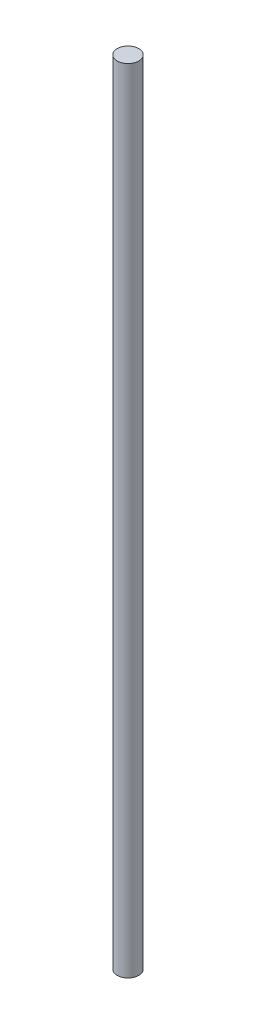
SolidWorks part; units mm, degrees
ref_plane "Front Plane" through (0, 0, 0) normal (0, 0, 1) x (1, 0, 0)
ref_plane "Top Plane" through (0, 0, 0) normal (0, 1, 0) x (1, 0, 0)
ref_plane "Right Plane" through (0, 0, 0) normal (1, 0, 0) x (0, 0, -1)
sketch "Sketch2" plane through (0, 0, 0) normal (0, 1, 0) x (1, 0, 0)
  circle A0 centre (0, 0) radius 1.075
  dimension "D1" = 2.15
extrude "Boss-Extrude1" add sketch "Sketch2" along normal blind 79
